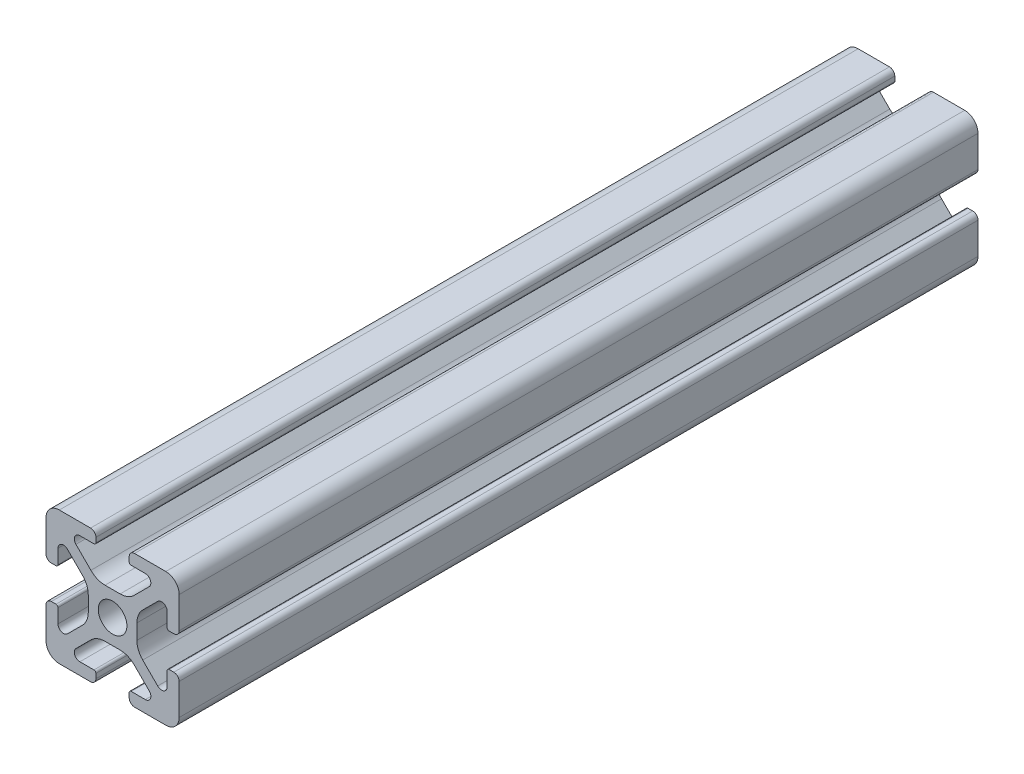
SolidWorks part; units mm, degrees
ref_plane "Front" through (0, 0, 0) normal (0, 0, 1) x (1, 0, 0)
ref_plane "Top" through (0, 0, 0) normal (0, 1, 0) x (1, 0, 0)
ref_plane "Right" through (0, 0, 0) normal (1, 0, 0) x (0, 0, -1)
sketch "Support-Front" plane through (0, 0, 0) normal (0, 0, 1) x (1, 0, 0)
  line L0 (10, 0) -> (-10, 0) construction
  line L1 (-10, -10) -> (10, -10)
  line L2 (-10, -10) -> (-10, 10)
  line L3 (-10, 10) -> (10, 10)
  line L4 (10, -10) -> (10, 10)
  line L5 (0, 10) -> (0, -10) construction
  dimension "Height-Profile" = 20
  dimension "Width-Profile" = 20
sketch "Support-Right-Length" plane through (0, 0, 0) normal (1, 0, 0) x (0, 0, -1)
  line L0 (0, -10) -> (0, 10) construction
  line L1 (-25, 10) -> (25, 10)
  line L2 (-25, 10) -> (-25, -10)
  line L3 (-25, -10) -> (25, -10)
  line L4 (25, 10) -> (25, -10)
  dimension "Length-Profile" = 50
sketch "Support-Profile" plane through (0, 0, 0) normal (0, 0, 1) x (1, 0, 0)
  line L8 (4.9176, -8.2) -> (2.8, -8.2)
  line L9 (2.5, -8.5) -> (2.5, -9.2)
  line L10 (3.3, -10) -> (8, -10)
  line L11 (10, -8) -> (10, -3.3)
  line L24 (9.2, -2.5) -> (8.5, -2.5)
  line L25 (8.2, -2.8) -> (8.2, -4.9176)
  line L26 (6.779, -5.5062) -> (4.5287, -3.2559)
  line L27 (3.65, -1.1346) -> (3.65, 1.1346)
  line L28 (4.5287, 3.2559) -> (6.779, 5.5062)
  line L29 (8.2, 4.9176) -> (8.2, 2.8)
  line L30 (8.5, 2.5) -> (9.2, 2.5)
  line L31 (10, 3.3) -> (10, 8)
  line L32 (8, 10) -> (3.3, 10)
  line L33 (2.5, 9.2) -> (2.5, 8.5)
  line L34 (2.8, 8.2) -> (4.9176, 8.2)
  line L35 (5.5062, 6.779) -> (3.2559, 4.5287)
  line L40 (1.1346, 3.65) -> (-1.1346, 3.65)
  line L41 (-3.2559, 4.5287) -> (-5.5062, 6.779)
  line L42 (-4.9176, 8.2) -> (-2.8, 8.2)
  line L43 (-2.5, 8.5) -> (-2.5, 9.2)
  line L44 (-3.3, 10) -> (-8, 10)
  line L45 (-10, 8) -> (-10, 3.3)
  line L46 (-9.2, 2.5) -> (-8.5, 2.5)
  line L47 (-8.2, 2.8) -> (-8.2, 4.9176)
  line L48 (-6.779, 5.5062) -> (-4.5287, 3.2559)
  line L49 (-3.65, 1.1346) -> (-3.65, -1.1346)
  line L50 (-4.5287, -3.2559) -> (-6.779, -5.5062)
  line L51 (-8.2, -4.9176) -> (-8.2, -2.8)
  line L52 (-8.5, -2.5) -> (-9.2, -2.5)
  line L53 (-10, -3.3) -> (-10, -8)
  line L54 (-8, -10) -> (-3.3, -10)
  line L55 (-2.5, -9.2) -> (-2.5, -8.5)
  line L56 (-2.8, -8.2) -> (-4.9176, -8.2)
  line L57 (-5.5062, -6.779) -> (-3.2559, -4.5287)
  line L58 (-1.1346, -3.65) -> (1.1346, -3.65)
  line L59 (3.2559, -4.5287) -> (5.5062, -6.779)
  circle A2 centre (0, 0) radius 2.15
  arc A3 (2.8, -8.2) -> (2.5, -8.5) centre (2.8, -8.5) ccw
  arc A5 (2.5, -9.2) -> (3.3, -10) centre (3.3, -9.2) ccw
  arc A24 (8, -10) -> (10, -8) centre (8, -8) ccw
  arc A25 (10, -3.3) -> (9.2, -2.5) centre (9.2, -3.3) ccw
  arc A26 (8.5, -2.5) -> (8.2, -2.8) centre (8.5, -2.8) ccw
  arc A27 (6.779, -5.5062) -> (8.2, -4.9176) centre (7.3676, -4.9176) ccw
  arc A28 (3.65, -1.1346) -> (4.5287, -3.2559) centre (6.65, -1.1346) ccw
  arc A29 (4.5287, 3.2559) -> (3.65, 1.1346) centre (6.65, 1.1346) ccw
  arc A30 (8.2, 4.9176) -> (6.779, 5.5062) centre (7.3676, 4.9176) ccw
  arc A31 (8.2, 2.8) -> (8.5, 2.5) centre (8.5, 2.8) ccw
  arc A32 (9.2, 2.5) -> (10, 3.3) centre (9.2, 3.3) ccw
  arc A33 (10, 8) -> (8, 10) centre (8, 8) ccw
  arc A34 (3.3, 10) -> (2.5, 9.2) centre (3.3, 9.2) ccw
  arc A35 (2.5, 8.5) -> (2.8, 8.2) centre (2.8, 8.5) ccw
  arc A38 (5.5062, 6.779) -> (4.9176, 8.2) centre (4.9176, 7.3676) ccw
  arc A39 (1.1346, 3.65) -> (3.2559, 4.5287) centre (1.1346, 6.65) ccw
  arc A44 (-3.2559, 4.5287) -> (-1.1346, 3.65) centre (-1.1346, 6.65) ccw
  arc A45 (-4.9176, 8.2) -> (-5.5062, 6.779) centre (-4.9176, 7.3676) ccw
  arc A46 (-2.8, 8.2) -> (-2.5, 8.5) centre (-2.8, 8.5) ccw
  arc A47 (-2.5, 9.2) -> (-3.3, 10) centre (-3.3, 9.2) ccw
  arc A48 (-8, 10) -> (-10, 8) centre (-8, 8) ccw
  arc A49 (-10, 3.3) -> (-9.2, 2.5) centre (-9.2, 3.3) ccw
  arc A50 (-8.5, 2.5) -> (-8.2, 2.8) centre (-8.5, 2.8) ccw
  arc A51 (-6.779, 5.5062) -> (-8.2, 4.9176) centre (-7.3676, 4.9176) ccw
  arc A52 (-3.65, 1.1346) -> (-4.5287, 3.2559) centre (-6.65, 1.1346) ccw
  arc A53 (-4.5287, -3.2559) -> (-3.65, -1.1346) centre (-6.65, -1.1346) ccw
  arc A54 (-8.2, -4.9176) -> (-6.779, -5.5062) centre (-7.3676, -4.9176) ccw
  arc A55 (-8.2, -2.8) -> (-8.5, -2.5) centre (-8.5, -2.8) ccw
  arc A56 (-9.2, -2.5) -> (-10, -3.3) centre (-9.2, -3.3) ccw
  arc A57 (-10, -8) -> (-8, -10) centre (-8, -8) ccw
  arc A58 (-3.3, -10) -> (-2.5, -9.2) centre (-3.3, -9.2) ccw
  arc A59 (-2.5, -8.5) -> (-2.8, -8.2) centre (-2.8, -8.5) ccw
  arc A60 (-5.5062, -6.779) -> (-4.9176, -8.2) centre (-4.9176, -7.3676) ccw
  arc A61 (-1.1346, -3.65) -> (-3.2559, -4.5287) centre (-1.1346, -6.65) ccw
  arc A62 (3.2559, -4.5287) -> (1.1346, -3.65) centre (1.1346, -6.65) ccw
  arc A63 (4.9176, -8.2) -> (5.5062, -6.779) centre (4.9176, -7.3676) ccw
ref_plane "Ref-Plane-1" through (0, 0, 25) normal (0, 0, 1) x (1, 0, 0)
ref_plane "Ref-Plane-2" through (0, 0, -25) normal (0, 0, 1) x (1, 0, 0)
sketch "Sketch4" plane through (0, 0, 25) normal (0, 0, 1) x (1, 0, 0)
  line L0 (-10, -10) -> (-10, 10) construction
  line L1 (-10, -10) -> (10, -10) construction
  line L2 (10, -10) -> (10, 10) construction
  line L3 (-10, 10) -> (10, 10) construction
  line L4 (-10, -10) -> (-10, 10)
  line L5 (-10, -10) -> (10, -10)
  line L6 (10, -10) -> (10, 10)
  line L7 (-10, 10) -> (10, 10)
extrude "Body" add sketch "Sketch4" against normal blind 120
sketch "Sketch16" plane through (0, 0, 0) normal (0, 0, 1) x (1, 0, 0)
  line L40 (4.9176, -8.2) -> (2.8, -8.2)
  line L41 (2.5, -8.5) -> (2.5, -9.2)
  line L42 (3.3, -10) -> (8, -10)
  line L43 (10, -8) -> (10, -3.3)
  line L44 (9.2, -2.5) -> (8.5, -2.5)
  line L45 (8.2, -2.8) -> (8.2, -4.9176)
  line L46 (6.779, -5.5062) -> (4.5287, -3.2559)
  line L47 (3.65, -1.1346) -> (3.65, 1.1346)
  line L48 (4.5287, 3.2559) -> (6.779, 5.5062)
  line L49 (8.2, 4.9176) -> (8.2, 2.8)
  line L50 (8.5, 2.5) -> (9.2, 2.5)
  line L51 (10, 3.3) -> (10, 8)
  line L52 (8, 10) -> (3.3, 10)
  line L53 (2.5, 9.2) -> (2.5, 8.5)
  line L54 (2.8, 8.2) -> (4.9176, 8.2)
  line L55 (5.5062, 6.779) -> (3.2559, 4.5287)
  line L56 (1.1346, 3.65) -> (-1.1346, 3.65)
  line L57 (-3.2559, 4.5287) -> (-5.5062, 6.779)
  line L58 (-4.9176, 8.2) -> (-2.8, 8.2)
  line L59 (-2.5, 8.5) -> (-2.5, 9.2)
  line L60 (-3.3, 10) -> (-8, 10)
  line L61 (-10, 8) -> (-10, 3.3)
  line L62 (-9.2, 2.5) -> (-8.5, 2.5)
  line L63 (-8.2, 2.8) -> (-8.2, 4.9176)
  line L64 (-6.779, 5.5062) -> (-4.5287, 3.2559)
  line L65 (-3.65, 1.1346) -> (-3.65, -1.1346)
  line L66 (-4.5287, -3.2559) -> (-6.779, -5.5062)
  line L67 (-8.2, -4.9176) -> (-8.2, -2.8)
  line L68 (-8.5, -2.5) -> (-9.2, -2.5)
  line L69 (-10, -3.3) -> (-10, -8)
  line L70 (-8, -10) -> (-3.3, -10)
  line L71 (-2.5, -9.2) -> (-2.5, -8.5)
  line L72 (-2.8, -8.2) -> (-4.9176, -8.2)
  line L73 (-5.5062, -6.779) -> (-3.2559, -4.5287)
  line L74 (-1.1346, -3.65) -> (1.1346, -3.65)
  line L75 (3.2559, -4.5287) -> (5.5062, -6.779)
  line L76 (4.9176, -8.2) -> (2.8, -8.2)
  line L77 (2.5, -8.5) -> (2.5, -9.2)
  line L78 (3.3, -10) -> (8, -10)
  line L79 (10, -8) -> (10, -3.3)
  line L80 (9.2, -2.5) -> (8.5, -2.5)
  line L81 (8.2, -2.8) -> (8.2, -4.9176)
  line L82 (6.779, -5.5062) -> (4.5287, -3.2559)
  line L83 (3.65, -1.1346) -> (3.65, 1.1346)
  line L84 (4.5287, 3.2559) -> (6.779, 5.5062)
  line L85 (8.2, 4.9176) -> (8.2, 2.8)
  line L86 (8.5, 2.5) -> (9.2, 2.5)
  line L87 (10, 3.3) -> (10, 8)
  line L88 (8, 10) -> (3.3, 10)
  line L89 (2.5, 9.2) -> (2.5, 8.5)
  line L90 (2.8, 8.2) -> (4.9176, 8.2)
  line L91 (5.5062, 6.779) -> (3.2559, 4.5287)
  line L92 (1.1346, 3.65) -> (-1.1346, 3.65)
  line L93 (-3.2559, 4.5287) -> (-5.5062, 6.779)
  line L94 (-4.9176, 8.2) -> (-2.8, 8.2)
  line L95 (-2.5, 8.5) -> (-2.5, 9.2)
  line L96 (-3.3, 10) -> (-8, 10)
  line L97 (-10, 8) -> (-10, 3.3)
  line L98 (-9.2, 2.5) -> (-8.5, 2.5)
  line L99 (-8.2, 2.8) -> (-8.2, 4.9176)
  line L100 (-6.779, 5.5062) -> (-4.5287, 3.2559)
  line L101 (-3.65, 1.1346) -> (-3.65, -1.1346)
  line L102 (-4.5287, -3.2559) -> (-6.779, -5.5062)
  line L103 (-8.2, -4.9176) -> (-8.2, -2.8)
  line L104 (-8.5, -2.5) -> (-9.2, -2.5)
  line L105 (-10, -3.3) -> (-10, -8)
  line L106 (-8, -10) -> (-3.3, -10)
  line L107 (-2.5, -9.2) -> (-2.5, -8.5)
  line L108 (-2.8, -8.2) -> (-4.9176, -8.2)
  line L109 (-5.5062, -6.779) -> (-3.2559, -4.5287)
  line L110 (-1.1346, -3.65) -> (1.1346, -3.65)
  line L111 (3.2559, -4.5287) -> (5.5062, -6.779)
  circle A7 centre (0, 0) radius 2.15 construction
  circle A8 centre (0, 0) radius 2.15
  arc A43 (2.8, -8.2) -> (2.5, -8.5) centre (2.8, -8.5) ccw
  arc A44 (2.5, -9.2) -> (3.3, -10) centre (3.3, -9.2) ccw
  arc A45 (8, -10) -> (10, -8) centre (8, -8) ccw
  arc A46 (10, -3.3) -> (9.2, -2.5) centre (9.2, -3.3) ccw
  arc A47 (8.5, -2.5) -> (8.2, -2.8) centre (8.5, -2.8) ccw
  arc A48 (6.779, -5.5062) -> (8.2, -4.9176) centre (7.3676, -4.9176) ccw
  arc A49 (3.65, -1.1346) -> (4.5287, -3.2559) centre (6.65, -1.1346) ccw
  arc A50 (4.5287, 3.2559) -> (3.65, 1.1346) centre (6.65, 1.1346) ccw
  arc A51 (8.2, 4.9176) -> (6.779, 5.5062) centre (7.3676, 4.9176) ccw
  arc A52 (8.2, 2.8) -> (8.5, 2.5) centre (8.5, 2.8) ccw
  arc A53 (9.2, 2.5) -> (10, 3.3) centre (9.2, 3.3) ccw
  arc A54 (10, 8) -> (8, 10) centre (8, 8) ccw
  arc A55 (3.3, 10) -> (2.5, 9.2) centre (3.3, 9.2) ccw
  arc A56 (2.5, 8.5) -> (2.8, 8.2) centre (2.8, 8.5) ccw
  arc A57 (5.5062, 6.779) -> (4.9176, 8.2) centre (4.9176, 7.3676) ccw
  arc A58 (1.1346, 3.65) -> (3.2559, 4.5287) centre (1.1346, 6.65) ccw
  arc A59 (-3.2559, 4.5287) -> (-1.1346, 3.65) centre (-1.1346, 6.65) ccw
  arc A60 (-4.9176, 8.2) -> (-5.5062, 6.779) centre (-4.9176, 7.3676) ccw
  arc A61 (-2.8, 8.2) -> (-2.5, 8.5) centre (-2.8, 8.5) ccw
  arc A62 (-2.5, 9.2) -> (-3.3, 10) centre (-3.3, 9.2) ccw
  arc A63 (-8, 10) -> (-10, 8) centre (-8, 8) ccw
  arc A64 (-10, 3.3) -> (-9.2, 2.5) centre (-9.2, 3.3) ccw
  arc A65 (-8.5, 2.5) -> (-8.2, 2.8) centre (-8.5, 2.8) ccw
  arc A66 (-6.779, 5.5062) -> (-8.2, 4.9176) centre (-7.3676, 4.9176) ccw
  arc A67 (-3.65, 1.1346) -> (-4.5287, 3.2559) centre (-6.65, 1.1346) ccw
  arc A68 (-4.5287, -3.2559) -> (-3.65, -1.1346) centre (-6.65, -1.1346) ccw
  arc A69 (-8.2, -4.9176) -> (-6.779, -5.5062) centre (-7.3676, -4.9176) ccw
  arc A70 (-8.2, -2.8) -> (-8.5, -2.5) centre (-8.5, -2.8) ccw
  arc A71 (-9.2, -2.5) -> (-10, -3.3) centre (-9.2, -3.3) ccw
  arc A72 (-10, -8) -> (-8, -10) centre (-8, -8) ccw
  arc A73 (-3.3, -10) -> (-2.5, -9.2) centre (-3.3, -9.2) ccw
  arc A74 (-2.5, -8.5) -> (-2.8, -8.2) centre (-2.8, -8.5) ccw
  arc A75 (-5.5062, -6.779) -> (-4.9176, -8.2) centre (-4.9176, -7.3676) ccw
  arc A76 (-1.1346, -3.65) -> (-3.2559, -4.5287) centre (-1.1346, -6.65) ccw
  arc A77 (3.2559, -4.5287) -> (1.1346, -3.65) centre (1.1346, -6.65) ccw
  arc A78 (4.9176, -8.2) -> (5.5062, -6.779) centre (4.9176, -7.3676) ccw
  arc A79 (2.8, -8.2) -> (2.5, -8.5) centre (2.8, -8.5) ccw
  arc A80 (2.5, -9.2) -> (3.3, -10) centre (3.3, -9.2) ccw
  arc A81 (8, -10) -> (10, -8) centre (8, -8) ccw
  arc A82 (10, -3.3) -> (9.2, -2.5) centre (9.2, -3.3) ccw
  arc A83 (8.5, -2.5) -> (8.2, -2.8) centre (8.5, -2.8) ccw
  arc A84 (6.779, -5.5062) -> (8.2, -4.9176) centre (7.3676, -4.9176) ccw
  arc A85 (3.65, -1.1346) -> (4.5287, -3.2559) centre (6.65, -1.1346) ccw
  arc A86 (4.5287, 3.2559) -> (3.65, 1.1346) centre (6.65, 1.1346) ccw
  arc A87 (8.2, 4.9176) -> (6.779, 5.5062) centre (7.3676, 4.9176) ccw
  arc A88 (8.2, 2.8) -> (8.5, 2.5) centre (8.5, 2.8) ccw
  arc A89 (9.2, 2.5) -> (10, 3.3) centre (9.2, 3.3) ccw
  arc A90 (10, 8) -> (8, 10) centre (8, 8) ccw
  arc A91 (3.3, 10) -> (2.5, 9.2) centre (3.3, 9.2) ccw
  arc A92 (2.5, 8.5) -> (2.8, 8.2) centre (2.8, 8.5) ccw
  arc A93 (5.5062, 6.779) -> (4.9176, 8.2) centre (4.9176, 7.3676) ccw
  arc A94 (1.1346, 3.65) -> (3.2559, 4.5287) centre (1.1346, 6.65) ccw
  arc A95 (-3.2559, 4.5287) -> (-1.1346, 3.65) centre (-1.1346, 6.65) ccw
  arc A96 (-4.9176, 8.2) -> (-5.5062, 6.779) centre (-4.9176, 7.3676) ccw
  arc A97 (-2.8, 8.2) -> (-2.5, 8.5) centre (-2.8, 8.5) ccw
  arc A98 (-2.5, 9.2) -> (-3.3, 10) centre (-3.3, 9.2) ccw
  arc A99 (-8, 10) -> (-10, 8) centre (-8, 8) ccw
  arc A100 (-10, 3.3) -> (-9.2, 2.5) centre (-9.2, 3.3) ccw
  arc A101 (-8.5, 2.5) -> (-8.2, 2.8) centre (-8.5, 2.8) ccw
  arc A102 (-6.779, 5.5062) -> (-8.2, 4.9176) centre (-7.3676, 4.9176) ccw
  arc A103 (-3.65, 1.1346) -> (-4.5287, 3.2559) centre (-6.65, 1.1346) ccw
  arc A104 (-4.5287, -3.2559) -> (-3.65, -1.1346) centre (-6.65, -1.1346) ccw
  arc A105 (-8.2, -4.9176) -> (-6.779, -5.5062) centre (-7.3676, -4.9176) ccw
  arc A106 (-8.2, -2.8) -> (-8.5, -2.5) centre (-8.5, -2.8) ccw
  arc A107 (-9.2, -2.5) -> (-10, -3.3) centre (-9.2, -3.3) ccw
  arc A108 (-10, -8) -> (-8, -10) centre (-8, -8) ccw
  arc A109 (-3.3, -10) -> (-2.5, -9.2) centre (-3.3, -9.2) ccw
  arc A110 (-2.5, -8.5) -> (-2.8, -8.2) centre (-2.8, -8.5) ccw
  arc A111 (-5.5062, -6.779) -> (-4.9176, -8.2) centre (-4.9176, -7.3676) ccw
  arc A112 (-1.1346, -3.65) -> (-3.2559, -4.5287) centre (-1.1346, -6.65) ccw
  arc A113 (3.2559, -4.5287) -> (1.1346, -3.65) centre (1.1346, -6.65) ccw
  arc A114 (4.9176, -8.2) -> (5.5062, -6.779) centre (4.9176, -7.3676) ccw
  dimension "D1" = 0
extrude "Cut-Profile" cut sketch "Sketch16" against normal through all and the other way through all flip side to cut
